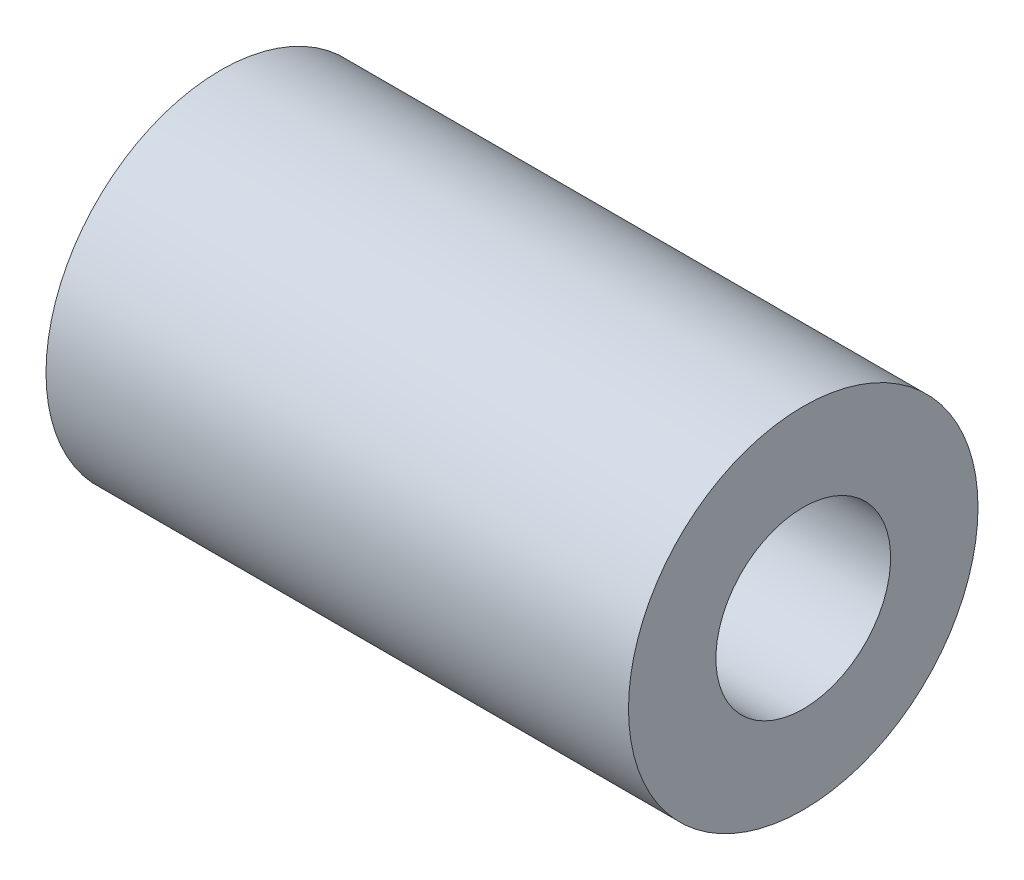
SolidWorks part; units mm, degrees
ref_plane "Plan de face" through (0, 0, 0) normal (0, 0, 1) x (1, 0, 0)
ref_plane "Plan de dessus" through (0, 0, 0) normal (0, 1, 0) x (1, 0, 0)
ref_plane "Plan de droite" through (0, 0, 0) normal (1, 0, 0) x (0, 0, -1)
sketch "Esquisse1" plane through (0, 0, 0) normal (0, 0, 1) x (1, 0, 0)
  line L0 (0, 0) -> (0, 6)
  line L1 (0, 6) -> (20, 6)
  line L2 (20, 6) -> (20, 3)
  line L3 (20, 3) -> (10, 3)
  line L4 (10, 3) -> (10, 0)
  line L5 (10, 0) -> (0, 0)
  dimension "D1" = 3
  dimension "D2" = 3
  dimension "D3" = 10
  dimension "D4" = 10
revolve "Révolution1" add sketch "Esquisse1" angle 360 about L5
